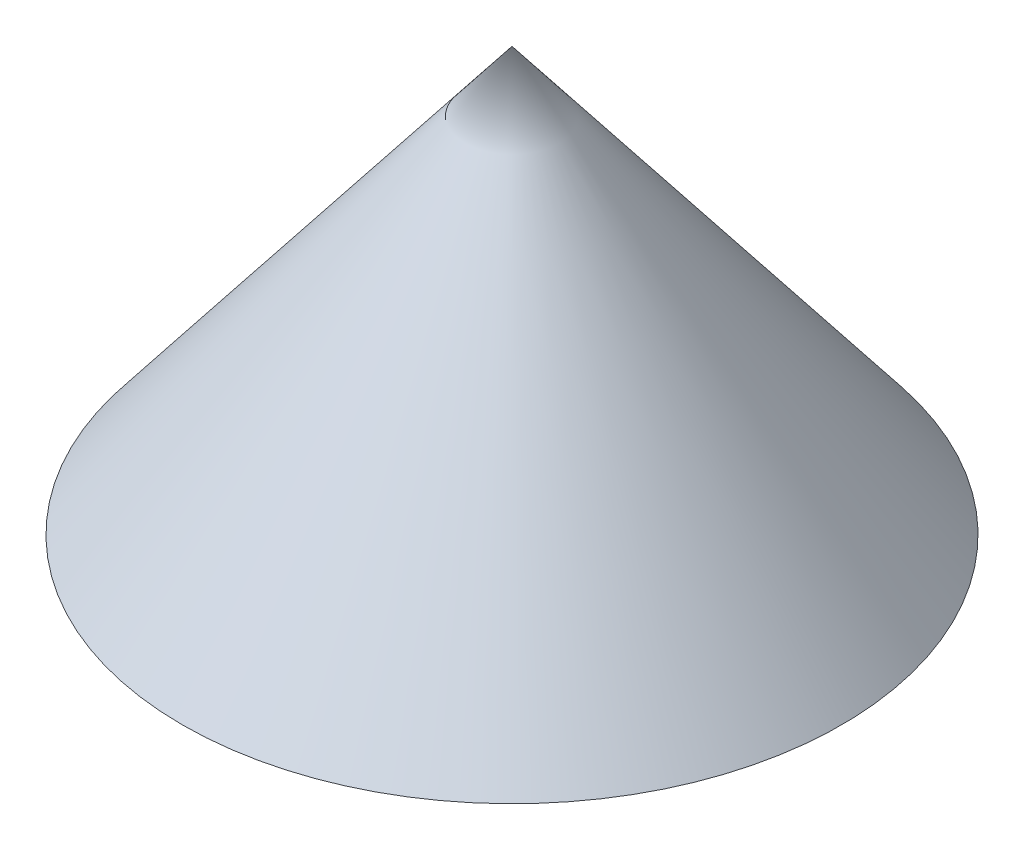
SolidWorks part; units mm, degrees
ref_plane "Front Plane" through (0, 0, 0) normal (0, 0, 1) x (1, 0, 0)
ref_plane "Top Plane" through (0, 0, 0) normal (0, 1, 0) x (1, 0, 0)
ref_plane "Right Plane" through (0, 0, 0) normal (1, 0, 0) x (0, 0, -1)
sketch "Sketch1" plane through (0, 0, 0) normal (0, 0, 1) x (1, 0, 0)
  line L0 (0, 0) -> (0, 55.5656)
  line L1 (0, 55.5656) -> (-43.2979, 0)
  line L2 (-43.2979, 0) -> (0, 0)
  line L3 (0, -16.2367) -> (0, 69.2766) construction
revolve "Revolve1" add sketch "Sketch1" angle 360 about L3
